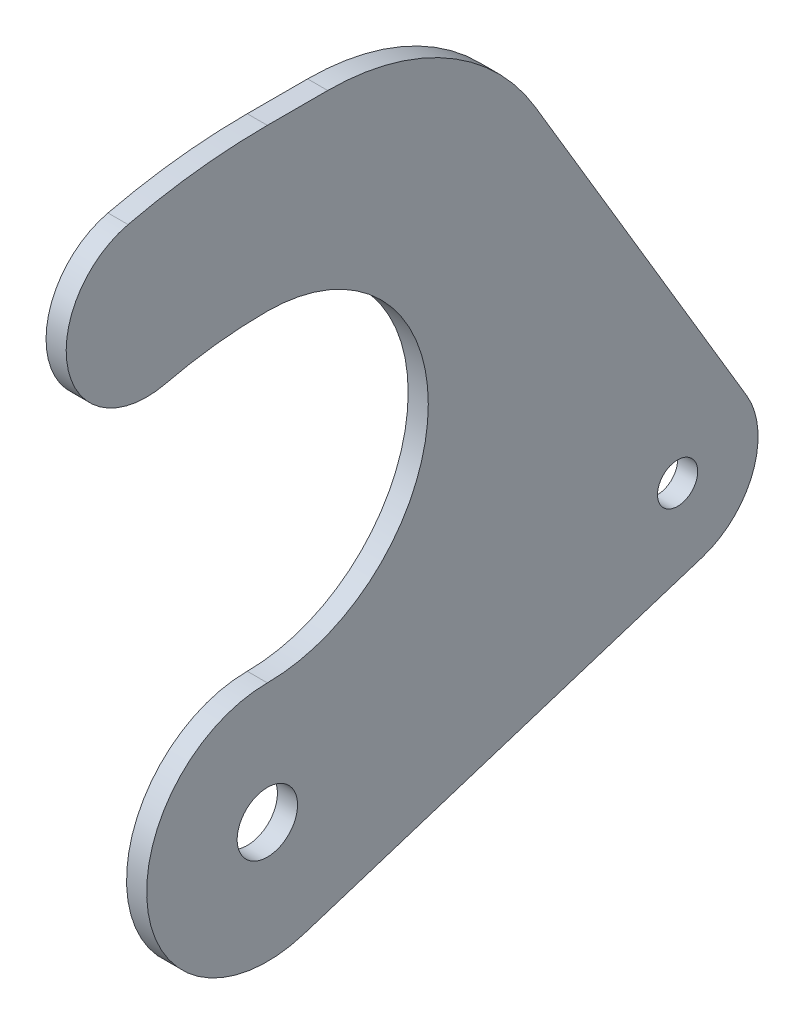
SolidWorks part; units mm, degrees
ref_plane "Front" through (0, 0, 0) normal (0, 0, 1) x (1, 0, 0)
ref_plane "Top" through (0, 0, 0) normal (0, 1, 0) x (1, 0, 0)
ref_plane "Right" through (0, 0, 0) normal (1, 0, 0) x (0, 0, -1)
sketch "Sketch1" plane through (0, 0, 0) normal (1, 0, 0) x (0, 0, -1)
  line L1 (5.7882, -18.1494) -> (68.6, 1.8824)
  line L2 (42.2739, 76.6211) -> (75.6575, 20.4724)
  line L3 (0, 95.25) -> (9.525, 95.25)
  line L4 (0, 0) -> (34.6131, -6.3297) construction
  line L5 (0, 0) -> (64.7412, 13.982) construction
  line L6 (0, 0) -> (55.6029, -35.9893) construction
  line L7 (0, 0) -> (-30.8092, 75.5249) construction
  line L8 (0, 0) -> (31.75, 75.1342) construction
  line L9 (37.2414, 8.0429) -> (31.9848, -20.7023) construction
  line L10 (-14.391, 35.2776) -> (14.8304, 35.0951) construction
  line L11 (0.2197, 35.1864) -> (0, 0) construction
  line L12 (55.6029, -35.9893) -> (19.05, -235.8746) construction
  line L13 (-22.225, 114.1317) -> (-22.225, -26.0995) construction
  circle A0 centre (0, 0) radius 4.7625
  circle A1 centre (0, 44.45) radius 21.082 construction
  arc A2 (0, 69.85) -> (0, 19.05) centre (0, 44.45) cw
  arc A3 (9.525, 95.25) -> (42.2739, 76.6211) centre (9.525, 57.15) cw
  circle A4 centre (0, 0) radius 19.05 construction
  circle A6 centre (64.7412, 13.982) radius 3.175
  arc A7 (68.6, 1.8824) -> (75.6575, 20.4724) centre (64.7412, 13.982) ccw
  arc A8 (5.7882, -18.1494) -> (0, 19.05) centre (0, 0) cw
  arc A10 (0, 95.25) -> (-21.9808, 92.6791) centre (0, 0) ccw
  arc A11 (-21.9808, 92.6791) -> (-16.1192, 67.9646) centre (-19.05, 80.3219) ccw
  arc A12 (0, 69.85) -> (-16.1192, 67.9646) centre (0, 0) ccw
  point P7 (-10.6947, 69.0265)
  point P10 (0, 0)
  point P33 (-30.7375, 75.2418)
  point P34 (0, 0)
  dimension "D1" = 42.164
  dimension "D2" = 9.525
  dimension "D3" = 25.4
  dimension "D4" = 38.1
  dimension "D11" = 38.1
  dimension "D12" = 12.7
  dimension "D14" = 6.35
  dimension "D16" = 19.05
  dimension "D5" = 50.8
  dimension "D6" = 38.1
  dimension "D7" = 38.1
  dimension "D8" = 95.25
  dimension "D10" = 31.75
  dimension "D13" = 9.525
  dimension "D15" = 203.2
  dimension "D17" = 235.8746
  dimension "D18" = 22.225
  dimension "D19" = 19.05
extrude "Boss-Extrude1" add sketch "Sketch1" along normal blind 3.175
